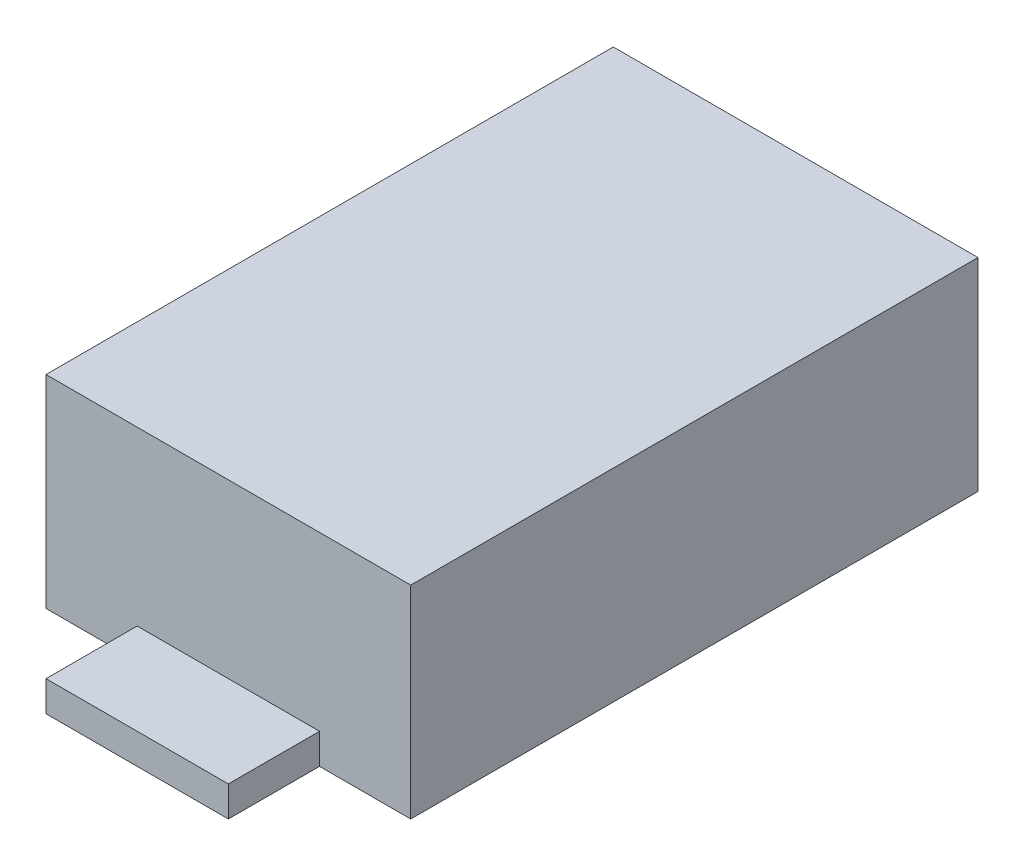
SolidWorks part; units mm, degrees
ref_plane "Front Plane" through (0, 0, 0) normal (0, 0, 1) x (1, 0, 0)
ref_plane "Top Plane" through (0, 0, 0) normal (0, 1, 0) x (1, 0, 0)
ref_plane "Right Plane" through (0, 0, 0) normal (1, 0, 0) x (0, 0, -1)
sketch "BaseS" plane through (0, 0, 0) normal (0, 1, 0) x (1, 0, 0)
  line L1 (-0.9, 1.4) -> (0.9, 1.4)
  line L2 (-0.9, 1.4) -> (-0.9, -1.4)
  line L3 (-0.9, -1.4) -> (0.9, -1.4)
  line L4 (0.9, 1.4) -> (0.9, -1.4)
  line L5 (-0.9, 1.4) -> (0.9, -1.4) construction
  line L6 (-0.9, -1.4) -> (0.9, 1.4) construction
  point P0 (0, 0)
  dimension "Width" = 1.8
  dimension "Length" = 2.8
extrude "Base" add sketch "BaseS" along normal blind 1
sketch "LegS" plane through (0, 0, 0) normal (0, 1, 0) x (1, 0, 0)
  line L0 (0.9, 1.4) -> (-0.9, 1.4) construction
  line L1 (-0.45, 1.4) -> (0.45, 1.4)
  line L2 (-0.45, 1.4) -> (-0.45, 1.85)
  line L3 (-0.45, 1.85) -> (0.45, 1.85)
  line L4 (0.45, 1.4) -> (0.45, 1.85)
  point P6 (0, 1.4)
  dimension "Length" = 0.45
  dimension "Width" = 0.9
extrude "Leg" add sketch "LegS" along normal blind 0.15
mirror "LVM" about plane through (0, 0, 0) normal (0, 0, 1) of "Leg"
